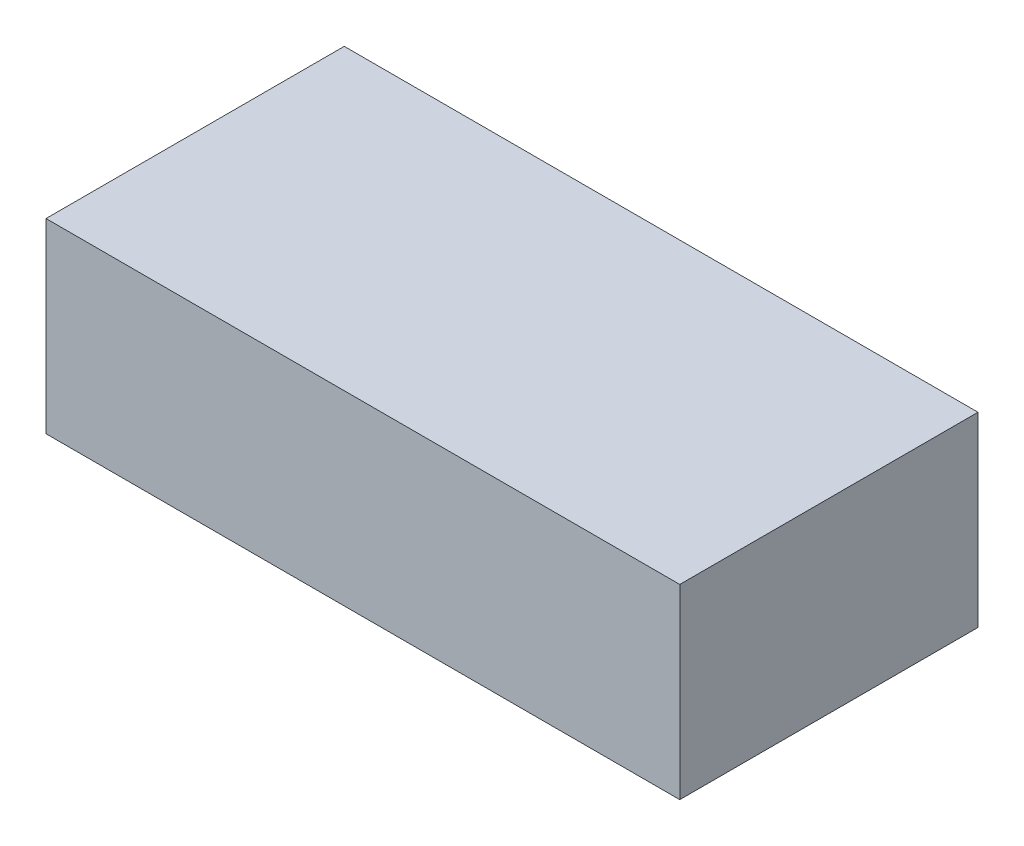
SolidWorks part; units mm, degrees
ref_plane "Front Plane" through (0, 0, 0) normal (0, 0, 1) x (1, 0, 0)
ref_plane "Top Plane" through (0, 0, 0) normal (0, 1, 0) x (1, 0, 0)
ref_plane "Right Plane" through (0, 0, 0) normal (1, 0, 0) x (0, 0, -1)
sketch "Sketch1" plane through (0, 0, 0) normal (0, 0, 1) x (1, 0, 0)
  line L1 (-6.0847, 129.8623) -> (163.9153, 129.8623)
  line L2 (-6.0847, 129.8623) -> (-6.0847, 79.8623)
  line L3 (-6.0847, 79.8623) -> (163.9153, 79.8623)
  line L4 (163.9153, 129.8623) -> (163.9153, 79.8623)
  dimension "D1" = 170
  dimension "D2" = 50
extrude "battery" add sketch "Sketch1" along normal blind 80
